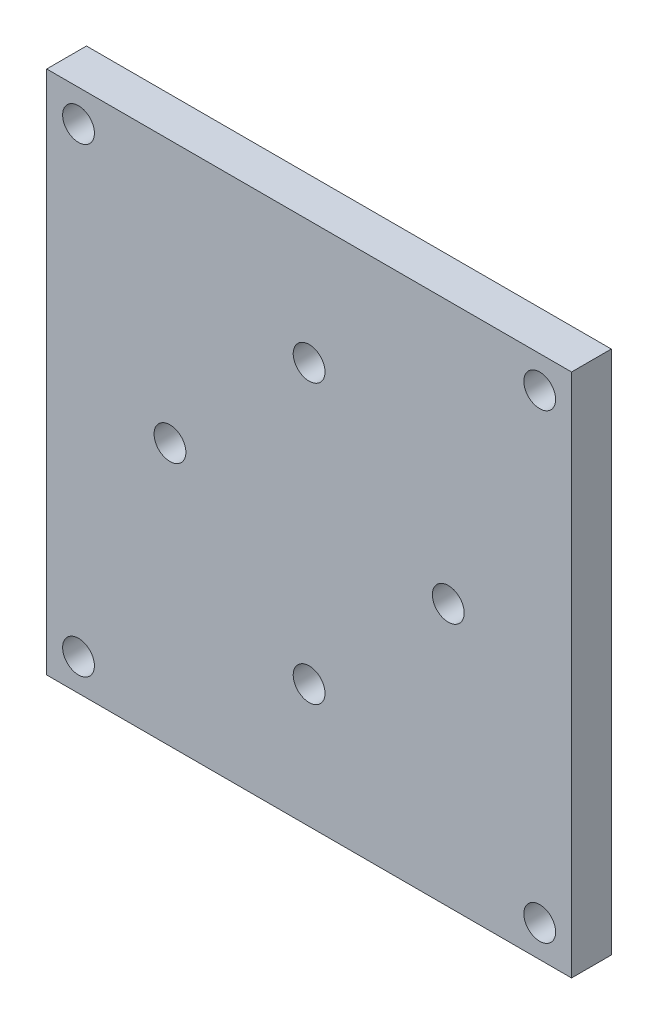
SolidWorks part; units mm, degrees
ref_plane "Front Plane" through (0, 0, 0) normal (0, 0, 1) x (1, 0, 0)
ref_plane "Top Plane" through (0, 0, 0) normal (0, 1, 0) x (1, 0, 0)
ref_plane "Right Plane" through (0, 0, 0) normal (1, 0, 0) x (0, 0, -1)
sketch "Sketch1" plane through (0, 0, 0) normal (0, 0, 1) x (1, 0, 0)
  line L1 (-33, -33) -> (33, -33)
  line L2 (-33, -33) -> (-33, 33)
  line L3 (-33, 33) -> (33, 33)
  line L4 (33, -33) -> (33, 33)
  line L5 (-33, -33) -> (33, 33) construction
  line L6 (-33, 33) -> (33, -33) construction
  point P0 (0, 0)
  dimension "D1" = 66
  dimension "D2" = 66
extrude "Boss-Extrude1" add sketch "Sketch1" along normal mid plane 5
sketch "Sketch2" plane through (0, 0, 2.5) normal (0, 0, 1) x (1, 0, 0)
  line L0 (-33, 33) -> (-33, -33) construction
  line L1 (-29, -29) -> (29, -29) construction
  line L2 (-29, -29) -> (-29, 29) construction
  line L3 (-29, 29) -> (29, 29) construction
  line L4 (29, -29) -> (29, 29) construction
  line L5 (-29, -29) -> (29, 29) construction
  line L6 (-29, 29) -> (29, -29) construction
  line L7 (33, 33) -> (-33, 33) construction
  circle A0 centre (-29, 29) radius 2
  circle A1 centre (29, 29) radius 2
  circle A2 centre (29, -29) radius 2
  circle A3 centre (-29, -29) radius 2
  point P0 (0, 0)
  dimension "D3" = 4
  dimension "D4" = 4
  dimension "D5" = 4
  dimension "D6" = 4
  dimension "D1" = 4
  dimension "D2" = 4
extrude "Cut-Extrude1" cut sketch "Sketch2" against normal through all
sketch "Sketch3" plane through (0, 0, 2.5) normal (0, 0, 1) x (1, 0, 0)
  circle A0 centre (0, 0) radius 17.5 construction
  circle A1 centre (0, 17.5) radius 2
  circle A2 centre (17.5, 0) radius 2
  circle A3 centre (0, -17.5) radius 2
  circle A4 centre (-17.5, 0) radius 2
  dimension "D1" = 35
  dimension "D2" = 4
  dimension "D3" = 4
  dimension "D4" = 4
  dimension "D5" = 4
extrude "Cut-Extrude2" cut sketch "Sketch3" against normal through all
